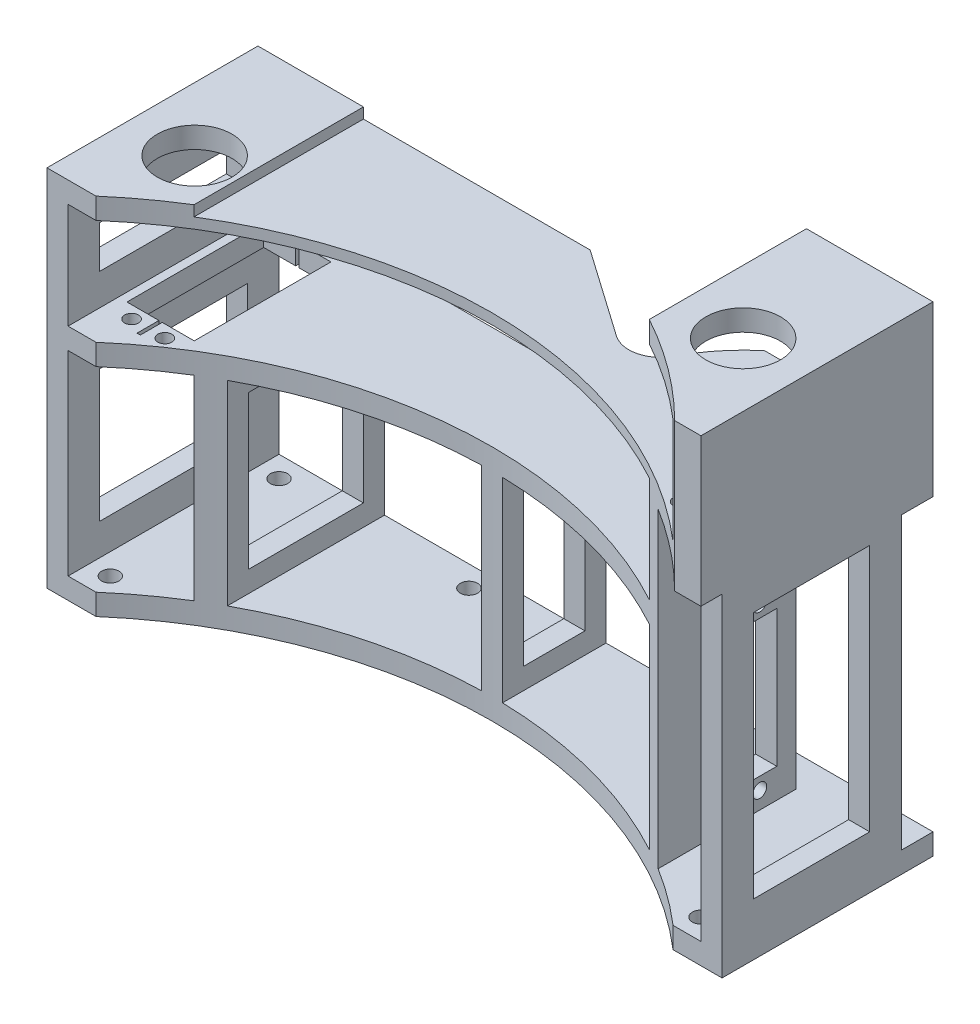
SolidWorks part; units mm, degrees
material "ABS"
ref_plane "Front Plane" through (0, 0, 0) normal (0, 0, 1) x (1, 0, 0)
ref_plane "Top Plane" through (0, 0, 0) normal (0, 1, 0) x (1, 0, 0)
ref_plane "Right Plane" through (0, 0, 0) normal (1, 0, 0) x (0, 0, -1)
sketch "Sketch1" plane through (0, 0, 0) normal (0, 0, 1) x (1, 0, 0)
  line L0 (-101.6, 106.425) -> (101.6, 106.425)
  line L1 (-101.6, 0) -> (101.6, 0)
  line L2 (-101.6, 0) -> (-101.6, 106.425)
  line L4 (101.6, 0) -> (101.6, 106.425)
  point P5 (0, 0)
  dimension "D1" = 203.2
  dimension "D2" = 106.425
extrude "Boss-Extrude1" add sketch "Sketch1" along normal mid plane 63.5
sketch "Sketch4" plane through (0, 0, -31.75) normal (0, 0, -1) x (-1, 0, 0)
  line L0 (-101.6, 0) -> (-101.6, 106.425) construction
  line L1 (101.6, 0) -> (101.6, 106.425) construction
  line L2 (-95.25, 103.25) -> (95.25, 103.25)
  line L3 (-95.25, 103.25) -> (-95.25, 71.5)
  line L4 (-95.25, 71.5) -> (95.25, 71.5)
  line L5 (95.25, 103.25) -> (95.25, 71.5)
  line L11 (-95.25, 65.15) -> (95.25, 65.15)
  line L12 (-95.25, 65.15) -> (-95.25, 6.35)
  line L13 (-95.25, 6.35) -> (95.25, 6.35)
  line L14 (95.25, 65.15) -> (95.25, 6.35)
  line L15 (101.6, 0) -> (-101.6, 0) construction
  dimension "D4" = 6.35
  dimension "D1" = 6.35
  dimension "D2" = 71.5
  dimension "D3" = 6.35
  dimension "D5" = 6.35
  dimension "D6" = 31.75
extrude "Cut-Extrude2" cut sketch "Sketch4" against normal through all
sketch "Sketch8" plane through (0, 0, 0) normal (0, 0, 1) x (1, 0, 0)
  line L0 (-95.25, 65.15) -> (95.25, 65.15) construction
  line L1 (-69.85, 65.15) -> (-63.5, 65.15)
  line L2 (-69.85, 65.15) -> (-69.85, 6.35)
  line L3 (-69.85, 6.35) -> (-63.5, 6.35)
  line L4 (-63.5, 65.15) -> (-63.5, 6.35)
  line L5 (95.25, 6.35) -> (-95.25, 6.35) construction
  line L6 (-95.25, 103.25) -> (95.25, 103.25) construction
  line L7 (63.5, 103.25) -> (69.85, 103.25)
  line L8 (63.5, 103.25) -> (63.5, 6.35)
  line L9 (63.5, 6.35) -> (69.85, 6.35)
  line L10 (69.85, 103.25) -> (69.85, 6.35)
  line L11 (95.25, 65.15) -> (95.25, 6.35) construction
  line L12 (-95.25, 6.35) -> (-95.25, 65.15) construction
  line L13 (-101.6, 0) -> (101.6, 0) construction
  line L14 (-3.175, 65.15) -> (3.175, 65.15)
  line L15 (-3.175, 65.15) -> (-3.175, 6.35)
  line L16 (-3.175, 6.35) -> (3.175, 6.35)
  line L17 (3.175, 65.15) -> (3.175, 6.35)
  point P24 (0, 0)
  point P25 (0, 6.35)
  dimension "D1" = 6.35
  dimension "D2" = 6.35
  dimension "D3" = 25.4
  dimension "D4" = 25.4
  dimension "D5" = 6.35
extrude "Boss-Extrude2" add sketch "Sketch8" along normal up to surface (63.5 mm away) from surface at -31.75 up to face at (0, 87.375, 31.75) starting at face at (0, 87.375, -31.75)
sketch "Sketch15" plane through (0, 103.25, 0) normal (0, -1, 0) x (1, 0, 0)
  line L4 (69.85, 31.75) -> (69.85, -31.75)
  line L5 (69.85, -31.75) -> (95.25, -31.75)
  line L6 (95.25, -31.75) -> (95.25, 31.75)
  line L7 (95.25, 31.75) -> (69.85, 31.75)
  line L8 (69.85, 31.75) -> (69.85, -31.75)
  line L9 (69.85, -31.75) -> (95.25, -31.75)
  line L10 (95.25, -31.75) -> (95.25, 31.75)
  line L11 (95.25, 31.75) -> (69.85, 31.75)
  dimension "D1" = 0
extrude "Boss-Extrude4" add sketch "Sketch15" along normal blind 3.175
sketch "Sketch2" plane through (0, 71.5, 0) normal (0, 1, 0) x (1, 0, 0)
  line L0 (-92.677, 24.55) -> (-72.423, -16.604) construction
  line L29 (-92.677, 24.55) -> (-83.05, 24.55)
  line L30 (-92.677, 24.55) -> (-92.677, -16.604)
  line L31 (-92.677, -16.604) -> (-83.05, -16.604)
  line L34 (-72.423, 24.55) -> (-72.423, -16.604)
  line L58 (69.85, 31.75) -> (69.85, -31.75)
  line L59 (69.85, -31.75) -> (95.25, -31.75)
  line L60 (95.25, -31.75) -> (95.25, 31.75)
  line L61 (95.25, 31.75) -> (69.85, 31.75)
  line L62 (69.85, 31.75) -> (69.85, -31.75)
  line L63 (69.85, -31.75) -> (95.25, -31.75)
  line L64 (95.25, -31.75) -> (95.25, 31.75)
  line L65 (95.25, 31.75) -> (69.85, 31.75)
  line L78 (-72.423, 24.55) -> (-92.677, -16.604) construction
  line L79 (-87.55, 28.273) -> (-77.55, -20.327) construction
  line L80 (-87.55, -20.327) -> (-77.55, 28.273) construction
  line L81 (-82.05, -16.604) -> (-72.423, -16.604)
  line L82 (-82.05, -16.604) -> (-82.05, -23.208)
  line L83 (-82.05, -23.208) -> (-83.05, -23.208)
  line L84 (-83.05, -16.604) -> (-83.05, -23.208)
  line L85 (-82.55, 3.973) -> (-13.3966, 3.973) construction
  line L86 (-82.05, 31.154) -> (-83.05, 31.154)
  line L87 (-82.05, 24.55) -> (-82.05, 31.154)
  line L88 (-83.05, 24.55) -> (-83.05, 31.154)
  line L89 (-82.05, 24.55) -> (-72.423, 24.55)
  line L90 (-101.6, -31.75) -> (101.6, -31.75) construction
  line L91 (-101.6, -31.75) -> (-101.6, 31.75) construction
  circle A12 centre (-87.55, -20.327) radius 2.1
  circle A13 centre (-77.55, -20.327) radius 2.1
  circle A14 centre (-87.55, 28.273) radius 2.1
  circle A15 centre (-77.55, 28.273) radius 2.1
  point P8 (-82.55, -23.208)
  point P17 (-82.55, 3.973)
  point P18 (-82.55, 3.973)
  point P27 (-82.55, -6.35)
  dimension "D3" = 48.6
  dimension "D4" = 4.2
  dimension "D2" = 10
  dimension "D5" = 41.154
  dimension "D6" = 20.254
  dimension "D7" = 1
  dimension "D8" = 6.604
  dimension "D9" = 30.9
  dimension "D10" = 25.4
  dimension "D11" = 0
  dimension "D12" = 19.05
extrude "Cut-Extrude3" cut sketch "Sketch2" against normal up to next
sketch "Sketch9" plane through (0, 106.425, 0) normal (0, 1, 0) x (1, 0, 0)
  line L0 (72.423, 24.55) -> (92.677, -16.604) construction
  line L1 (72.423, 24.55) -> (82.05, 24.55)
  line L2 (72.423, 24.55) -> (72.423, -16.604)
  line L3 (72.423, -16.604) -> (82.05, -16.604)
  line L4 (92.677, 24.55) -> (92.677, -16.604)
  line L5 (92.677, 24.55) -> (72.423, -16.604) construction
  line L6 (77.55, 28.273) -> (87.55, -20.327) construction
  line L7 (77.55, -20.327) -> (87.55, 28.273) construction
  line L8 (83.05, -16.604) -> (92.677, -16.604)
  line L9 (83.05, -16.604) -> (83.05, -23.208)
  line L10 (83.05, -23.208) -> (82.05, -23.208)
  line L11 (82.05, -16.604) -> (82.05, -23.208)
  line L12 (82.55, 3.973) -> (164.4034, 3.973) construction
  line L13 (83.05, 31.154) -> (82.05, 31.154)
  line L14 (83.05, 24.55) -> (83.05, 31.154)
  line L15 (82.05, 24.55) -> (82.05, 31.154)
  line L16 (83.05, 24.55) -> (92.677, 24.55)
  line L17 (101.6, -31.75) -> (101.6, 31.75) construction
  line L19 (-101.6, -31.75) -> (101.6, -31.75) construction
  circle A0 centre (77.55, -20.327) radius 2.1
  circle A1 centre (87.55, -20.327) radius 2.1
  circle A2 centre (77.55, 28.273) radius 2.1
  circle A3 centre (87.55, 28.273) radius 2.1
  point P8 (82.55, -23.208)
  point P17 (82.55, 3.973)
  point P18 (82.55, 3.973)
  point P27 (82.55, -6.35)
  dimension "D3" = 4.2
  dimension "D1" = 10
  dimension "D2" = 48.6
  dimension "D4" = 41.154
  dimension "D5" = 20.254
  dimension "D6" = 1
  dimension "D7" = 6.604
  dimension "D8" = 30.9
  dimension "D9" = 19.05
  dimension "D10" = 25.4
extrude "Cut-Extrude4" cut sketch "Sketch9" against normal up to next
sketch "Sketch12" plane through (0, 0, 0) normal (0, 1, 0) x (1, 0, 0)
  line L0 (-63.5, -31.75) -> (-63.5, 31.75) construction
  line L1 (-69.85, -31.75) -> (-95.25, -31.75) construction
  line L2 (-95.25, -31.75) -> (-95.25, 31.75) construction
  line L3 (-101.6, 31.75) -> (101.6, 31.75) construction
  circle A0 centre (-88.9, 25.4) radius 2.6
  circle A1 centre (-88.9, -25.4) radius 2.6
  circle A2 centre (-31.75, 25.4) radius 2.6
  dimension "D1" = 5.2
  dimension "D2" = 6.35
  dimension "D3" = 6.35
  dimension "D4" = 6.35
  dimension "D5" = 31.75
extrude "Cut-Extrude7" cut sketch "Sketch12" along normal up to surface (6.35 mm away) and the other way through all up to face at (-33.3375, 6.35, 0)
mirror "Mirror1" about plane through (0, 0, 0) normal (1, 0, 0) of "Cut-Extrude7"
sketch "Sketch16" plane through (0, 106.425, 0) normal (0, 1, 0) x (1, 0, 0)
  line L2 (-69.85, 31.75) -> (-101.6, 31.75)
  line L3 (-101.6, 31.75) -> (-101.6, -31.75)
  line L12 (-101.6, -31.75) -> (-69.85, -31.75)
  line L13 (-69.85, 31.75) -> (-69.85, -31.75)
  dimension "D1" = 31.75
extrude "Boss-Extrude5" add sketch "Sketch16" along normal blind 3.175
sketch "Sketch17" plane through (0, 109.6, 0) normal (0, 1, 0) x (1, 0, 0)
  line L0 (-101.6, -31.75) -> (-69.85, -31.75) construction
  line L1 (-101.6, 31.75) -> (-101.6, -31.75) construction
  circle A0 centre (-82.55, -6.35) radius 11.2395
  dimension "D3" = 22.479
  dimension "D1" = 25.4
  dimension "D2" = 19.05
extrude "Cut-Extrude8" cut sketch "Sketch17" against normal up to next
sketch "Sketch18" plane through (0, 106.425, 0) normal (0, 1, 0) x (1, 0, 0)
  line L5 (101.6, -31.75) -> (101.6, 31.75) construction
  line L6 (-69.85, -31.75) -> (101.6, -31.75) construction
  line L14 (101.6, -31.75) -> (101.6, 31.75)
  line L15 (101.6, 31.75) -> (95.25, 31.75)
  line L16 (95.25, -31.75) -> (95.25, 31.75)
  line L22 (95.25, -31.75) -> (82.55, -31.75)
  line L23 (101.6, -31.75) -> (101.6, -38.1)
  line L24 (101.6, -38.1) -> (82.55, -38.1)
  line L25 (82.55, -31.75) -> (82.55, -38.1)
  dimension "D4" = 6.35
  dimension "D5" = 19.05
extrude "Boss-Extrude6" add sketch "Sketch18" along normal blind 38.1 from surface at -6.35 starting at face at (87.55, 100.075, 18.227)
sketch "Sketch20" plane through (0, 138.175, 0) normal (0, 1, 0) x (1, 0, 0)
  line L1 (63.5, 31.75) -> (101.6, 31.75)
  line L2 (63.5, 31.75) -> (63.5, -38.1)
  line L3 (63.5, -38.1) -> (101.6, -38.1)
  line L4 (101.6, 31.75) -> (101.6, -38.1)
  line L6 (-69.85, -31.75) -> (82.55, -31.75) construction
  circle A0 centre (82.55, -6.35) radius 11.2395
  dimension "D2" = 19.05
  dimension "D1" = 22.479
  dimension "D4" = 38.1
  dimension "D3" = 25.4
extrude "Boss-Extrude7" add sketch "Sketch20" along normal blind 6.35
sketch "Sketch10" plane through (0, 106.425, 0) normal (0, 1, 0) x (1, 0, 0)
  circle A3 centre (0, -132.08) radius 131.1117 construction
  circle A4 centre (0, -132.08) radius 131.1117 construction
  circle A5 centre (0, -132.08) radius 132.6992
  dimension "D1" = 1.5875
extrude "Cut-Extrude5" cut sketch "Sketch10" against normal through all both and the other way through all
sketch "Sketch21" plane through (0, 106.425, 0) normal (0, 1, 0) x (1, 0, 0)
  line L5 (34.6759, 6.35) -> (-1.5991, 31.75)
  line L6 (-69.85, 31.75) -> (95.25, 31.75) construction
  line L7 (-1.5991, 31.75) -> (50.9018, 31.75)
  arc A1 (34.6759, 6.35) -> (50.9018, 31.75) centre (82.55, -6.35) cw
  dimension "D2" = 49.53
  dimension "D1" = 35
  dimension "D3" = 25.4
extrude "Cut-Extrude10" cut sketch "Sketch21" against normal up to surface (3.175 mm away) up to face at (-82.55, 103.25, 17.5895)
sketch "Sketch23" plane through (0, 0, -31.75) normal (0, 0, -1) x (-1, 0, 0)
  line L1 (-101.6, 6.35) -> (-57.15, 6.35)
  line L2 (-101.6, 6.35) -> (-101.6, 93.725)
  line L3 (-101.6, 93.725) -> (-57.15, 93.725)
  line L4 (-57.15, 6.35) -> (-57.15, 93.725)
  line L7 (-63.5, 71.5) -> (95.25, 71.5) construction
  line L9 (-63.5, 65.15) -> (-63.5, 6.35) construction
  line L10 (-101.6, 0) -> (-101.6, 144.525) construction
  line L11 (-63.5, 6.35) -> (-3.175, 6.35) construction
  dimension "D1" = 6.35
  dimension "D2" = 22.225
extrude "Cut-Extrude11" cut sketch "Sketch23" against normal blind 9.525
sketch "Sketch24" plane through (63.5, 0, 0) normal (-1, 0, 0) x (0, 0, 1)
  line L0 (-16.477, 56.354) -> (3.777, 15.2) construction
  line L1 (-16.477, 56.354) -> (-6.85, 56.354)
  line L2 (-16.477, 56.354) -> (-16.477, 15.2)
  line L3 (-16.477, 15.2) -> (-6.85, 15.2)
  line L4 (3.777, 56.354) -> (3.777, 15.2)
  line L5 (3.777, 56.354) -> (-16.477, 15.2) construction
  line L6 (-11.35, 60.077) -> (-1.35, 11.477) construction
  line L7 (-11.35, 11.477) -> (-1.35, 60.077) construction
  line L8 (-5.85, 15.2) -> (3.777, 15.2)
  line L9 (-5.85, 15.2) -> (-5.85, 8.596)
  line L10 (-5.85, 8.596) -> (-6.85, 8.596)
  line L11 (-6.85, 15.2) -> (-6.85, 8.596)
  line L12 (-6.35, 35.777) -> (65.4757, 35.777) construction
  line L13 (-5.85, 62.958) -> (-6.85, 62.958)
  line L14 (-5.85, 56.354) -> (-5.85, 62.958)
  line L15 (-6.85, 56.354) -> (-6.85, 62.958)
  line L16 (-5.85, 56.354) -> (3.777, 56.354)
  line L17 (-22.225, 65.15) -> (-22.225, 6.35) construction
  line L18 (15.5603, 65.15) -> (-22.225, 65.15) construction
  circle A0 centre (-11.35, 11.477) radius 2.1
  circle A1 centre (-1.35, 11.477) radius 2.1
  circle A2 centre (-11.35, 60.077) radius 2.1
  circle A3 centre (-1.35, 60.077) radius 2.1
  point P8 (-6.35, 8.596)
  point P17 (-6.35, 35.777)
  point P18 (-6.35, 35.777)
  point P27 (-6.35, 46.1)
  dimension "D3" = 4.2
  dimension "D1" = 10
  dimension "D2" = 48.6
  dimension "D4" = 41.154
  dimension "D5" = 20.254
  dimension "D6" = 1
  dimension "D7" = 6.604
  dimension "D8" = 30.9
  dimension "D9" = 15.875
  dimension "D10" = 19.05
extrude "Cut-Extrude12" cut sketch "Sketch24" against normal up to next
sketch "Sketch26" plane through (95.25, 0, 0) normal (-1, 0, 0) x (0, 0, 1)
  line L12 (-12.7, 90.55) -> (-12.7, 15.875)
  line L13 (-12.7, 15.875) -> (22.225, 15.875)
  line L14 (22.225, 15.875) -> (22.225, 90.55)
  line L15 (22.225, 90.55) -> (-12.7, 90.55)
  line L16 (-12.7, 90.55) -> (-12.7, 15.875)
  line L17 (-12.7, 15.875) -> (22.225, 15.875)
  line L18 (22.225, 15.875) -> (22.225, 90.55)
  line L19 (22.225, 90.55) -> (-12.7, 90.55)
  dimension "D1" = 9.525
extrude "Cut-Extrude13" cut sketch "Sketch26" against normal up to next
sketch "Sketch27" plane through (63.5, 0, 0) normal (-1, 0, 0) x (0, 0, 1)
  line L6 (9.2103, 77.85) -> (9.2103, 96.9)
  line L8 (9.2103, 77.85) -> (9.2103, 96.9)
  line L12 (-15.875, 96.9) -> (-15.875, 77.85)
  line L13 (-15.875, 77.85) -> (9.2103, 77.85)
  line L15 (9.2103, 96.9) -> (-15.875, 96.9)
  line L16 (-15.875, 96.9) -> (-15.875, 77.85)
  line L17 (-15.875, 77.85) -> (9.2103, 77.85)
  line L19 (9.2103, 96.9) -> (-15.875, 96.9)
  dimension "D1" = 6.35
extrude "Cut-Extrude14" cut sketch "Sketch27" against normal up to next
sketch "Sketch28" plane through (3.175, 0, 0) normal (1, 0, 0) x (0, 0, -1)
  line L8 (25.4, 58.8) -> (6.9313, 58.8)
  line L9 (6.9313, 58.8) -> (6.9313, 12.7)
  line L10 (6.9313, 12.7) -> (25.4, 12.7)
  line L11 (25.4, 12.7) -> (25.4, 58.8)
  line L12 (25.4, 58.8) -> (6.9313, 58.8)
  line L13 (6.9313, 58.8) -> (6.9313, 12.7)
  line L14 (6.9313, 12.7) -> (25.4, 12.7)
  line L15 (25.4, 12.7) -> (25.4, 58.8)
  dimension "D1" = 6.35
extrude "Cut-Extrude15" cut sketch "Sketch28" against normal up to next
sketch "Sketch29" plane through (-63.5, 0, 0) normal (1, 0, 0) x (0, 0, -1)
  line L8 (25.4, 58.8) -> (-9.2103, 58.8)
  line L9 (-9.2103, 58.8) -> (-9.2103, 12.7)
  line L10 (-9.2103, 12.7) -> (25.4, 12.7)
  line L11 (25.4, 12.7) -> (25.4, 58.8)
  line L12 (25.4, 58.8) -> (-9.2103, 58.8)
  line L13 (-9.2103, 58.8) -> (-9.2103, 12.7)
  line L14 (-9.2103, 12.7) -> (25.4, 12.7)
  line L15 (25.4, 12.7) -> (25.4, 58.8)
  dimension "D1" = 6.35
extrude "Cut-Extrude16" cut sketch "Sketch29" against normal up to next
sketch "Sketch30" plane through (-95.25, 0, 0) normal (1, 0, 0) x (0, 0, -1)
  line L8 (22.225, 15.875) -> (22.225, 55.625)
  line L9 (22.225, 55.625) -> (-22.225, 55.625)
  line L10 (-22.225, 55.625) -> (-22.225, 15.875)
  line L11 (-22.225, 15.875) -> (22.225, 15.875)
  line L12 (22.225, 15.875) -> (22.225, 55.625)
  line L13 (22.225, 55.625) -> (-22.225, 55.625)
  line L14 (-22.225, 55.625) -> (-22.225, 15.875)
  line L15 (-22.225, 15.875) -> (22.225, 15.875)
  dimension "D1" = 9.525
extrude "Cut-Extrude17" cut sketch "Sketch30" against normal up to next
sketch "Sketch31" plane through (-95.25, 0, 0) normal (1, 0, 0) x (0, 0, -1)
  line L4 (22.225, 81.025) -> (22.225, 93.725)
  line L6 (22.225, 81.025) -> (22.225, 93.725)
  line L9 (22.225, 93.725) -> (-22.225, 93.725)
  line L10 (-22.225, 93.725) -> (-22.225, 81.025)
  line L11 (-22.225, 81.025) -> (22.225, 81.025)
  line L13 (22.225, 93.725) -> (-22.225, 93.725)
  line L14 (-22.225, 93.725) -> (-22.225, 81.025)
  line L15 (-22.225, 81.025) -> (22.225, 81.025)
  dimension "D1" = 9.525
extrude "Cut-Extrude18" cut sketch "Sketch31" against normal up to next
fillet "Fillet1" radius 9.525 1 edges at (34.6759, 104.8375, -6.35)
equation "\"tightTol\"= 0.005in"
equation "\"normTol\"= 0.01in"
equation "\"looseTol\"= 0.02in"
equation "\"D1@Sketch12\"=5.2mm"
equation "\"D2@Sketch1\"=8mm+0.5+3.25+0.125"
equation "\"D2@Sketch4\"=8mm+0.25+2.25"
equation "\"D3@Sketch17\" = 7 / 8 + \"normTol\""
equation "\"D1@Sketch20\"=7/8+\"normTol\""
